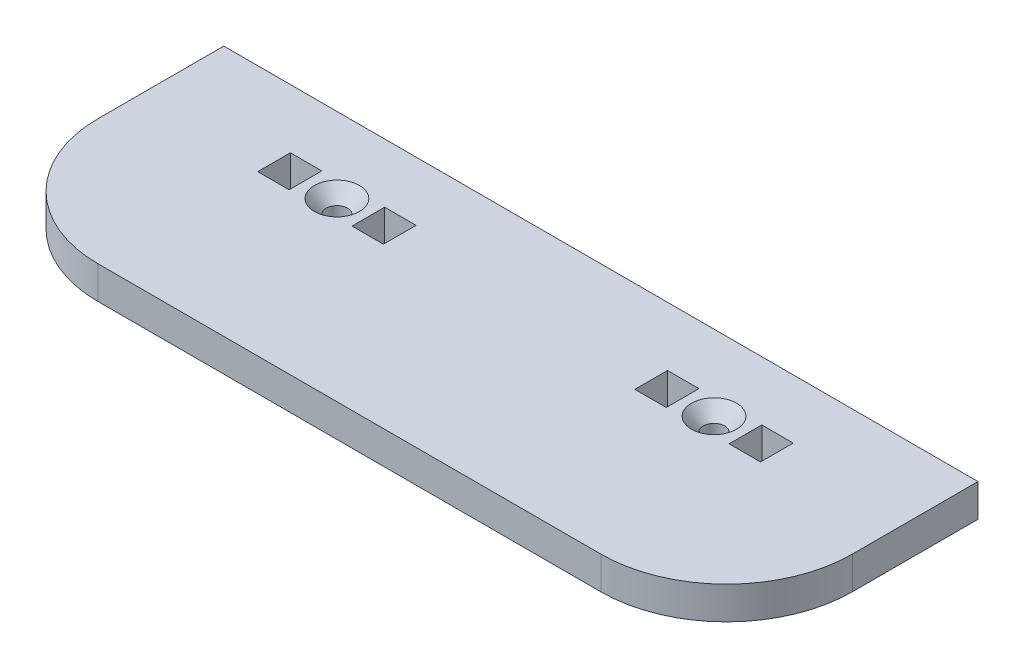
SolidWorks part; units mm, degrees
material "Acrylic (BLUE)"
ref_plane "Front Plane" through (0, 0, 0) normal (0, 0, 1) x (1, 0, 0)
ref_plane "Top Plane" through (0, 0, 0) normal (0, 1, 0) x (1, 0, 0)
ref_plane "Right Plane" through (0, 0, 0) normal (1, 0, 0) x (0, 0, -1)
sketch "Sketch1" plane through (0, 0, 0) normal (0, 1, 0) x (1, 0, 0)
  line L0 (-76.2, 25.4) -> (76.2, -25.4) construction
  line L1 (-76.2, 25.4) -> (76.2, 25.4)
  line L2 (-76.2, 25.4) -> (-76.2, -25.4)
  line L3 (-76.2, -25.4) -> (76.2, -25.4)
  line L4 (76.2, 25.4) -> (76.2, -25.4)
  dimension "D1" = 152.4
  dimension "D2" = 50.8
extrude "Boss-Extrude1" add sketch "Sketch1" along normal blind 6.604
fillet "Fillet1" radius 25.4 2 edges at (76.2, 3.302, 25.4) (-76.2, 3.302, 25.4)
sketch "Sketch2" plane through (0, 6.604, 0) normal (0, 1, 0) x (1, 0, 0)
  line L0 (76.2, 25.4) -> (-76.2, 25.4) construction
  line L1 (-50.8, 13.462) -> (-76.2, 13.462) construction
  line L2 (-76.2, 25.4) -> (-76.2, 0) construction
  line L3 (50.8, 13.462) -> (76.2, 13.462) construction
  line L4 (76.2, 0) -> (76.2, 25.4) construction
  line B0 (-31.75, 13.462) -> (-25.4, 13.462)
  line B1 (-25.4, 13.462) -> (-25.4, 6.858)
  line B2 (-25.4, 6.858) -> (-31.75, 6.858)
  line B3 (-31.75, 6.858) -> (-31.75, 13.462)
  line B4 (-50.8, 13.462) -> (-44.45, 13.462)
  line B5 (-44.45, 13.462) -> (-44.45, 6.858)
  line B6 (-44.45, 6.858) -> (-50.8, 6.858)
  line B7 (-50.8, 6.858) -> (-50.8, 13.462)
  circle B8 centre (-38.1, 10.16) radius 2.1526
  line B9 (-38.1, 10.16) -> (-44.45, 10.16) construction
  line B10 (44.45, 13.462) -> (50.8, 13.462)
  line B11 (50.8, 13.462) -> (50.8, 6.858)
  line B12 (50.8, 6.858) -> (44.45, 6.858)
  line B13 (44.45, 6.858) -> (44.45, 13.462)
  line B14 (25.4, 13.462) -> (31.75, 13.462)
  line B15 (31.75, 13.462) -> (31.75, 6.858)
  line B16 (31.75, 6.858) -> (25.4, 6.858)
  line B17 (25.4, 6.858) -> (25.4, 13.462)
  circle B18 centre (38.1, 10.16) radius 2.1526
  dimension "D1" = 15.24
  dimension "D2" = 76.2
sketch_block_instance "BOLT_HOLE-1"
sketch_block "BOLT_HOLE" parameters "D1"=4.3053, "D2"=6.35, "D3"=6.35, "D4"=6.604
sketch_block_instance "BOLT_HOLE-2"
extrude "Cut-Extrude1" cut sketch "Sketch2" against normal through all
hole_wizard "CSK for #8 Flat Head Socket Cap Screw1" positions "Sketch4" profile "Sketch3" countersink size "#8" standard "ANSI Inch" end condition through all
sketch "Sketch4" plane through (0, 6.604, 0) normal (0, 1, 0) x (1, 0, 0)
  point P0 (-38.1, 10.16)
  point P3 (38.1, 10.16)
sketch "Sketch3" plane through (-38.1, 6.604, -10.16) normal (1, 0, 0) x (0, 0, 1)
  line L0 (0, 0) -> (0, 6.604)
  line L1 (0, 6.604) -> (2.1526, 6.604)
  line L2 (2.1526, 6.604) -> (2.1526, 2.7685)
  line L3 (2.1526, 2.7685) -> (4.5593, 0)
  line L5 (4.5593, 0) -> (0, 0)
  line L6 (-2.1526, 2.7685) -> (-4.5593, 0) construction
  line L11 (0, -6.35) -> (0, 107.95) construction
  dimension "Thru Hole Dia." = 4.3053
  dimension "Thru Hole Depth" = 6.604
  dimension "Near C'Sink Dia." = 9.1186
  dimension "Near C'Sink Angle" = 82
other "Move Face1" [suppressed] parameters "D1"=0.0508
